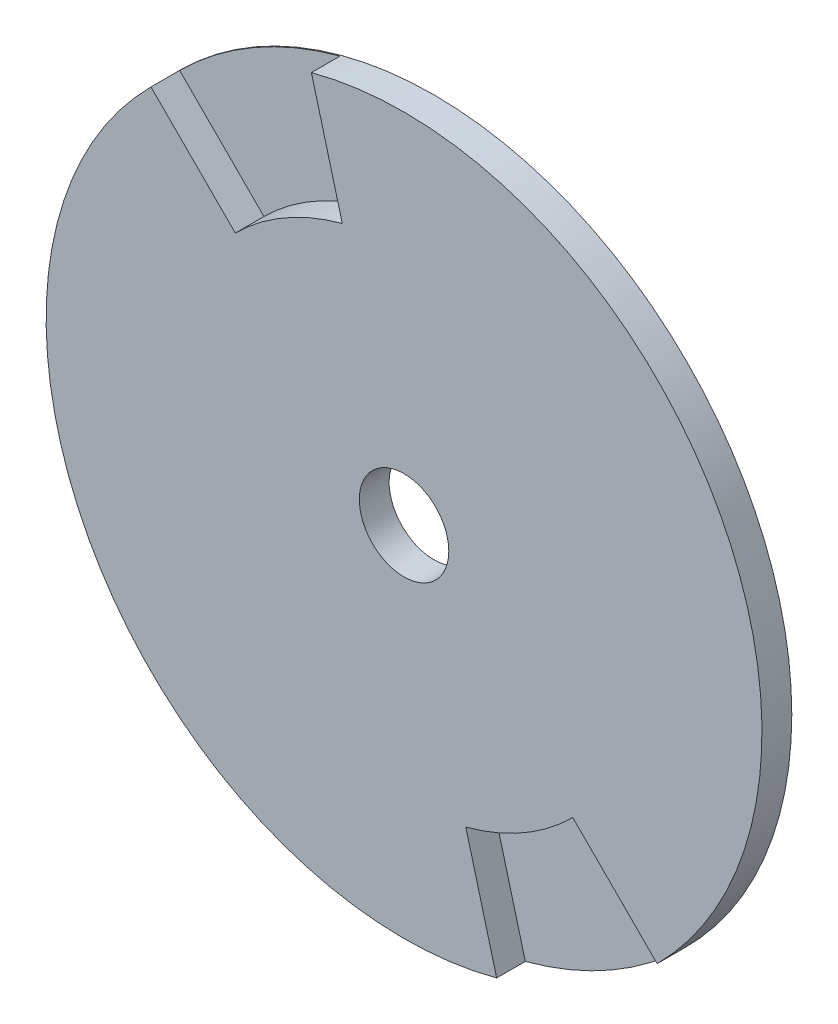
SolidWorks part; units mm, degrees
ref_plane "Front Plane" through (0, 0, 0) normal (0, 0, 1) x (1, 0, 0)
ref_plane "Top Plane" through (0, 0, 0) normal (0, 1, 0) x (1, 0, 0)
ref_plane "Right Plane" through (0, 0, 0) normal (1, 0, 0) x (0, 0, -1)
sketch "Sketch1" plane through (0, 0, 0) normal (0, 0, 1) x (1, 0, 0)
  circle A0 centre (0, 0) radius 19.05
  dimension "D1" = 38.1
extrude "Extrude1" add sketch "Sketch1" along normal blind 1.5875
sketch "Sketch2" plane through (0, 0, 1.5875) normal (0, 0, 1) x (1, 0, 0)
  line L2 (0, 0) -> (29.31, 29.31) construction
  circle A0 centre (0, 0) radius 2.3813
  dimension "D1" = 4.7625
extrude "Cut-Extrude1" cut sketch "Sketch2" against normal blind 3.175
sketch "Sketch3" plane through (0, 0, 1.5875) normal (0, 0, 1) x (1, 0, 0)
  line L0 (0, 0) -> (0, 22.1008) construction
  line L1 (0, 0) -> (-13.4704, 13.4704) construction
  line L2 (0, 0) -> (-4.9305, 18.4009) construction
  line L3 (0, 0) -> (32.7205, 18.8912) construction
  line L4 (0, 0) -> (-30.5221, -17.6219) construction
  line L5 (0, 0) -> (7.2901, -17.5999) construction
  line L6 (0, 0) -> (11.5969, -15.1134) construction
  line L7 (-13.4704, 13.4704) -> (-8.9803, 8.9803)
  line L8 (-4.9305, 18.4009) -> (-3.287, 12.2673)
  line L9 (13.4704, -13.4704) -> (8.9803, -8.9803)
  line L10 (4.9305, -18.4009) -> (3.287, -12.2673)
  line L11 (0, 0) -> (-9.525, 16.4978) construction
  circle A0 centre (0, 0) radius 12.7 construction
  circle A1 centre (0, 0) radius 19.05 construction
  arc A2 (-13.4704, 13.4704) -> (-4.9305, 18.4009) centre (0, 0) cw
  arc A3 (-8.9803, 8.9803) -> (-3.287, 12.2673) centre (0, 0) cw
  arc A4 (4.9305, -18.4009) -> (13.4704, -13.4704) centre (0, 0) ccw
  arc A5 (3.287, -12.2673) -> (8.9803, -8.9803) centre (0, 0) ccw
  circle M3 centre (0, 0) radius 19.05
  dimension "D2" = 38.1
  dimension "D3" = 25.4
  dimension "D1" = 60
  dimension "D4" = 30
  dimension "D5" = 15
extrude "Cut-Extrude2" cut sketch "Sketch3" against normal blind 1.524 contours L7 A3 L8 M3 | A5 L10 L9 M3
